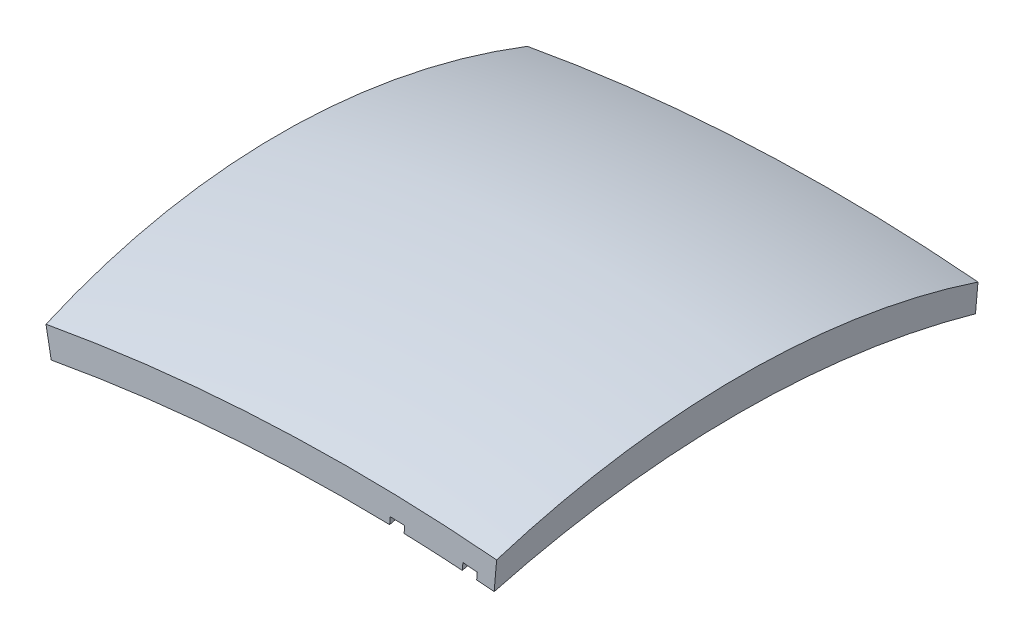
SolidWorks part; units mm, degrees
material "Alloy Steel"
ref_plane "Front Plane" through (0, 0, 0) normal (0, 0, 1) x (1, 0, 0)
ref_plane "Top Plane" through (0, 0, 0) normal (0, 1, 0) x (1, 0, 0)
ref_plane "Right Plane" through (0, 0, 0) normal (1, 0, 0) x (0, 0, -1)
sketch "Sketch1" plane through (0, 0, 0) normal (0, 0, 1) x (1, 0, 0)
  arc A0 (-890.2857, 339.5469) -> (29.9143, 382.891) centre (-269.2285, -3055.9223) cw
  point P4 (29.5311, 339.4766)
  dimension "D1" = 3451.8
  dimension "D2" = 920.2
ref_plane "Plane1" through (-890.2857, 339.5469, 0) normal (-0.9837, -0.1799, 0) x (0, 0, 1)
sketch "Sketch3" plane through (-890.2857, 339.5469, 0) normal (-0.9837, -0.1799, 0) x (0, 0, 1)
  line L2 (0, 0) -> (0, 60)
  line L4 (-1000, 0) -> (-1000, 60)
  arc A0 (0, 60) -> (-1000, 60) centre (-500, -1354.2136) ccw
  arc A1 (-1000, 0) -> (0, 0) centre (-500, -1654.2136) cw
  dimension "D3" = 1500
  dimension "D5" = 300
  dimension "D1" = 1000
  dimension "D2" = 60
  dimension "D4" = 60
sweep "Sweep1" add profiles "Sketch3" path "Sketch1"
sketch "Sketch4" plane through (0, 0, 0) normal (0, 0, 1) x (1, 0, 0)
  line L10 (-185.8616, 409.8455) -> (-187.1615, 394.9019)
  line L12 (-155.8218, 409.0003) -> (-157.1217, 394.0567)
  line L14 (29.9143, 382.891) -> (35.1141, 442.6653) construction
  line L15 (29.9143, 382.891) -> (35.1141, 442.6653)
  arc A1 (29.9143, 382.891) -> (-890.2857, 339.5469) centre (-269.2285, -3055.9223) ccw construction
  arc A3 (-185.8616, 409.8455) -> (-155.8218, 409.0003) centre (-267.9186, -3040.9791) cw
  arc A4 (-187.1615, 394.9019) -> (-157.1217, 394.0567) centre (-171.916, 402.5003) ccw
  dimension "D9" = 187.3
  dimension "D4" = 30
  dimension "D5" = 15
  dimension "D8" = 15
ref_plane "Plane3" through (-205.3754, 17.8656, 0) normal (0.9962, -0.0867, 0) x (0, 0, -1)
sketch "Sketch19" plane through (-205.3754, 17.8656, 0) normal (0.9962, -0.0867, 0) x (0, 0, -1)
  line L0 (70, 529.6909) -> (70, 279.1407) construction
  arc A0 (1000, 384.0429) -> (0, 384.0429) centre (500, -1270.1707) ccw construction
  arc A1 (70, 403.6043) -> (0, 384.0429) centre (500, -1270.1707) ccw
  point P5 (500, 279.1407)
  dimension "D1" = 70
sweep "Cut-Sweep1" cut profiles "Sketch4" path "Sketch19"
sketch "Sketch22" plane through (0, 0, 0) normal (0, 0, 1) x (1, 0, 0)
  line L0 (-6.3654, 385.8543) -> (-5.1042, 400.3528)
  line L1 (-5.1042, 400.3528) -> (-34.9913, 402.9527)
  line L2 (-34.9913, 402.9527) -> (-36.2913, 388.0091)
  line L4 (29.9143, 382.891) -> (35.1141, 442.6653) construction
  arc A0 (29.9143, 382.891) -> (-157.1217, 394.0567) centre (-269.2285, -3055.9223) ccw construction
  arc A1 (-36.2913, 388.0091) -> (-6.3654, 385.8543) centre (-20.3802, 400.0996) ccw
  dimension "D1" = 15
  dimension "D2" = 30
  dimension "D3" = 36.4
ref_plane "Plane5" through (-54.7704, 4.7645, 0) normal (0.9962, -0.0867, 0) x (0, 0, -1)
sketch "Sketch24" plane through (-54.7704, 4.7645, 0) normal (0.9962, -0.0867, 0) x (0, 0, -1)
  line L0 (70, 465.725) -> (70, 308.7375) construction
  arc A0 (1000, 384.0429) -> (0, 384.0429) centre (500, -1270.1707) ccw construction
  arc A1 (70, 403.6043) -> (0, 384.0429) centre (500, -1270.1707) ccw
  dimension "D1" = 70
sweep "Cut-Sweep6" cut profiles "Sketch22" path "Sketch24"
ref_plane "Plane6" through (0, 0, -500) normal (0, 0, 1) x (1, 0, 0)
mirror "Mirror1" about plane through (0, 0, -500) normal (0, 0, 1) of "Cut-Sweep1", "Cut-Sweep6"
